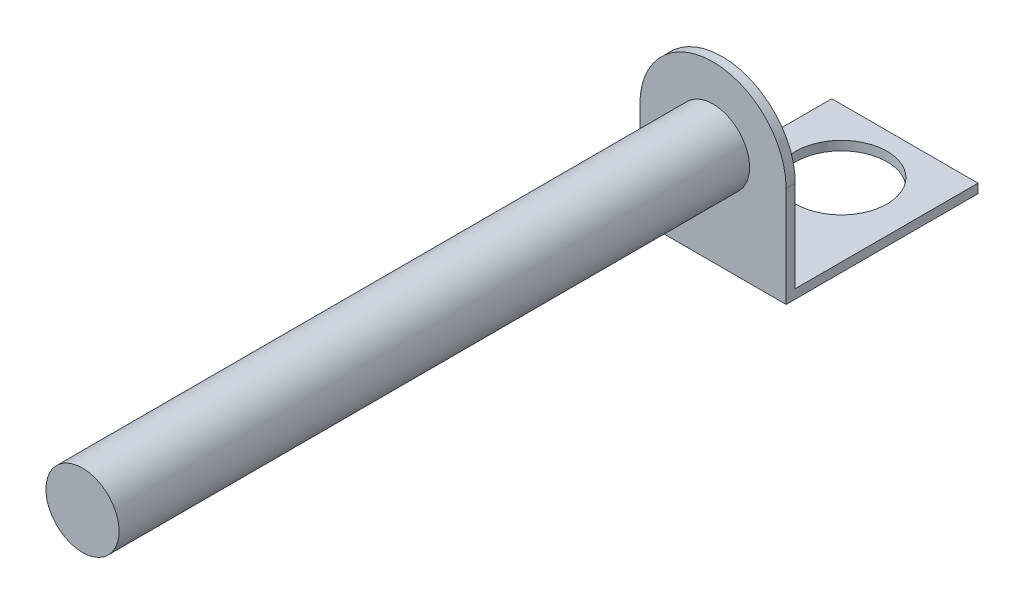
SolidWorks part; units mm, degrees
ref_plane "Front Plane" through (0, 0, 0) normal (0, 0, 1) x (1, 0, 0)
ref_plane "Top Plane" through (0, 0, 0) normal (0, 1, 0) x (1, 0, 0)
ref_plane "Right Plane" through (0, 0, 0) normal (1, 0, 0) x (0, 0, -1)
sketch "Sketch1" plane through (0, 0, 0) normal (0, 0, 1) x (1, 0, 0)
  circle A0 centre (0, 0) radius 4
  dimension "D1" = 8
extrude "Boss-Extrude1" add sketch "Sketch1" along normal blind 69
sketch "Sketch2" plane through (0, 0, 0) normal (0, 0, -1) x (-1, 0, 0)
  line L0 (-8, 0) -> (-8, -10)
  line L1 (-8, -10) -> (8, -10)
  line L2 (8, -10) -> (8, 0)
  arc A0 (-8, 0) -> (8, 0) centre (0, 0) cw
  dimension "D1" = 16
extrude "Boss-Extrude2" add sketch "Sketch2" along normal blind 1
sketch "Sketch3" plane through (0, -10, 0) normal (0, -1, 0) x (1, 0, 0)
  line L0 (-8, -1) -> (8, -1)
  line L1 (8, -1) -> (8, -21)
  line L2 (8, -21) -> (-8, -21)
  line L3 (-8, -21) -> (-8, -1)
  dimension "D1" = 20
extrude "Boss-Extrude3" add sketch "Sketch3" along normal blind 1 separate body
sketch "Sketch4" plane through (0, 0, -1) normal (0, 0, 1) x (1, 0, 0)
  line L0 (-8, -10) -> (-8, -11)
  line L1 (-8, -11) -> (8, -11)
  line L2 (8, -11) -> (8, -10) construction
  line L3 (8, -11) -> (-8, -11) construction
  line L4 (8, -11) -> (8, -10)
  line L5 (8, -10) -> (-8, -10)
extrude "Boss-Extrude4" add sketch "Sketch4" along normal blind 1
sketch "Sketch5" plane through (0, -10, 0) normal (0, 1, 0) x (1, 0, 0)
  circle A0 centre (0, 14.0462) radius 5
  dimension "D1" = 10
extrude "Cut-Extrude1" cut sketch "Sketch5" against normal blind 1 contours A0
